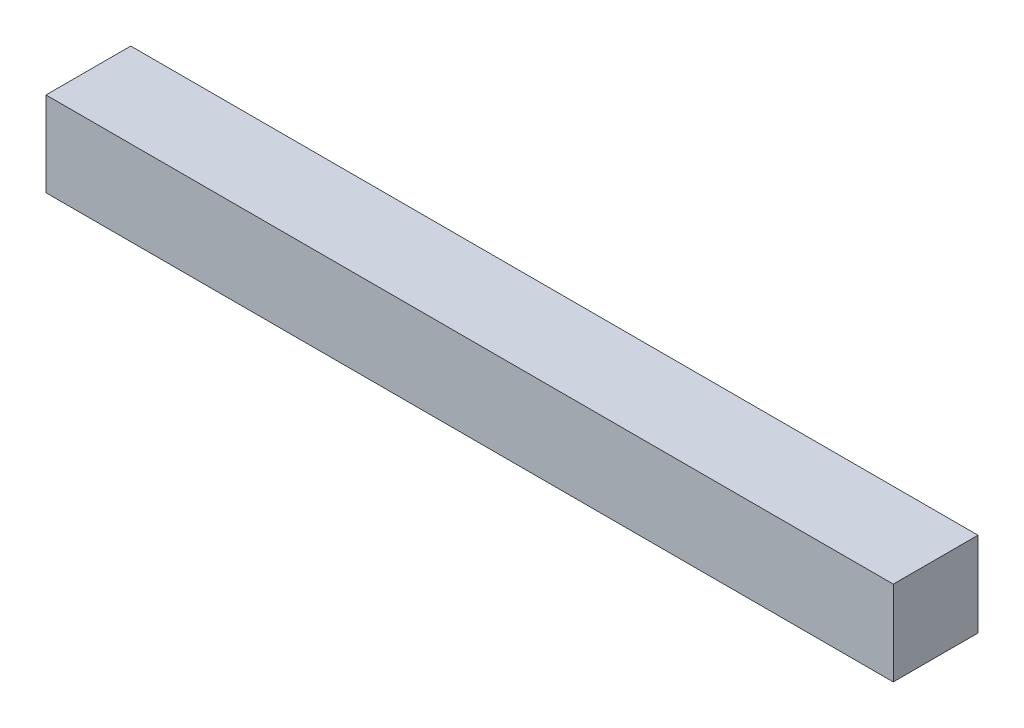
SolidWorks part; units mm, degrees
ref_plane "Front" through (0, 0, 0) normal (0, 0, 1) x (1, 0, 0)
ref_plane "Top" through (0, 0, 0) normal (0, 1, 0) x (1, 0, 0)
ref_plane "Right" through (0, 0, 0) normal (1, 0, 0) x (0, 0, -1)
sketch "Croquis1" plane through (0, 0, 0) normal (1, 0, 0) x (0, 0, -1)
  line L1 (-15, 15) -> (15, 15)
  line L2 (-15, 15) -> (-15, -15)
  line L3 (-15, -15) -> (15, -15)
  line L4 (15, 15) -> (15, -15)
  line L5 (-15, 15) -> (15, -15) construction
  line L6 (-15, -15) -> (15, 15) construction
  point P0 (0, 0)
  dimension "D1" = 30
extrude "Saliente-Extruir1" add sketch "Croquis1" along normal mid plane 300
